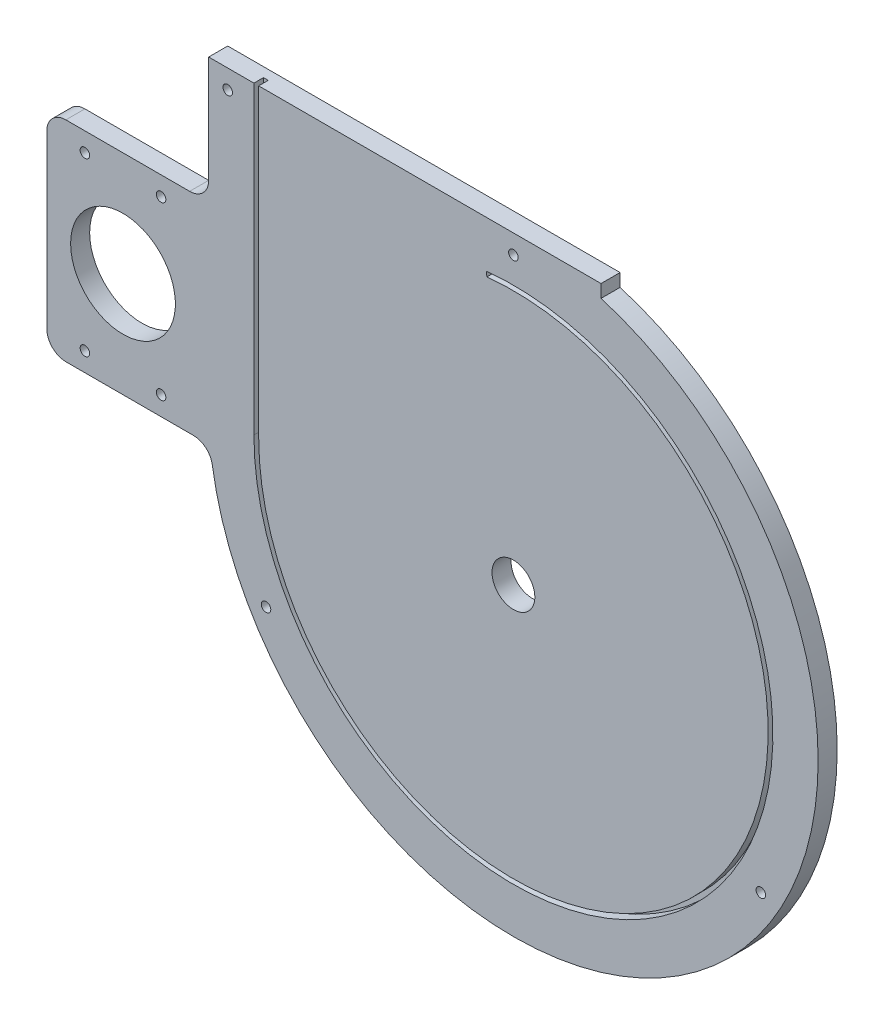
SolidWorks part; units mm, degrees
ref_plane "Front Plane" through (0, 0, 0) normal (0, 0, 1) x (1, 0, 0)
ref_plane "Top Plane" through (0, 0, 0) normal (0, 1, 0) x (1, 0, 0)
ref_plane "Right Plane" through (0, 0, 0) normal (1, 0, 0) x (0, 0, -1)
sketch "Sketch1" plane through (0, 0, 0) normal (0, 0, 1) x (1, 0, 0)
  line L1 (203.2, -203.2) -> (-203.2, -203.2)
  line L2 (203.2, -203.2) -> (203.2, 203.2)
  line L3 (203.2, 203.2) -> (-203.2, 203.2)
  line L4 (-203.2, -203.2) -> (-203.2, 203.2)
  line L5 (203.2, -203.2) -> (-203.2, 203.2) construction
  line L6 (203.2, 203.2) -> (-203.2, -203.2) construction
  circle A0 centre (0, 0) radius 14.2875
  circle A1 centre (0, 0) radius 160.3375 construction
  circle A2 centre (0, 0) radius 50.8 construction
  point P0 (0, 0)
  dimension "D3" = 28.575
  dimension "D4" = 101.6
  dimension "D1" = 406.4
  dimension "D2" = 406.4
  dimension "D5" = 203.2
  dimension "D6" = 203.2
extrude "Boss-Extrude1" add sketch "Sketch1" along normal blind 12.7
sketch "Sketch2" plane through (0, 0, 12.7) normal (0, 0, 1) x (1, 0, 0)
  line L0 (-18.0277, 172.0958) -> (-17.6969, 168.9381)
  line L1 (-173.0375, 0) -> (-173.0375, 203.2)
  line L2 (-169.8625, 0) -> (-169.8625, 203.2)
  line L3 (-169.8625, 203.2) -> (-173.0375, 203.2)
  line L4 (203.2, 203.2) -> (-203.2, 203.2) construction
  line L5 (0, 0) -> (-139.4589, -105.0957) construction
  arc A0 (-18.0277, 172.0958) -> (-173.0375, 0) centre (0, 0) cw
  arc A1 (-17.6969, 168.9381) -> (-169.8625, 0) centre (0, 0) cw
  circle A2 centre (0, 0) radius 14.2875 construction
  circle A3 centre (0, 0) radius 50.8 construction
  circle A4 centre (-90.0144, -67.8345) radius 61.9125 construction
  circle A5 centre (0, 0) radius 169.8625 construction
  point P13 (-138.1911, -104.1403)
  dimension "D2" = 101.6
  dimension "D3" = 123.825
  dimension "D4" = 1.5875
  dimension "D1" = 3.175
extrude "Cut-Extrude1" cut sketch "Sketch2" against normal blind 6.35
sketch "Sketch3" plane through (0, 0, 12.7) normal (0, 0, 1) x (1, 0, 0)
  line L0 (-203.2, 203.2) -> (-203.2, -203.2) construction
  line L1 (58.4327, 194.6172) -> (58.4327, 203.2)
  line L2 (203.2, 203.2) -> (-169.8625, 203.2) construction
  line L3 (58.4327, 203.2) -> (203.2, 203.2)
  line L4 (-203.2, -203.2) -> (203.2, -203.2) construction
  line L5 (203.2, -203.2) -> (203.2, 203.2) construction
  line L6 (-203.2, 0) -> (-203.2, -203.2)
  line L7 (-203.2, -203.2) -> (203.2, -203.2)
  line L8 (203.2, -203.2) -> (203.2, 203.2)
  arc A0 (-203.2, 0) -> (58.4327, 194.6172) centre (0, 0) ccw
  line M4 (-203.2, 203.2) -> (-203.2, -203.2)
  line M5 (-203.2, -203.2) -> (203.2, -203.2)
  line M6 (203.2, -203.2) -> (203.2, 203.2)
  line M7 (203.2, 203.2) -> (-169.8625, 203.2)
extrude "Cut-Extrude2" cut sketch "Sketch3" against normal through all contours A0 L8 L1 M7 | A0 L7 M6 | A0 M4 M5
sketch "Sketch4" plane through (0, 0, 12.7) normal (0, 0, 1) x (1, 0, 0)
  line L0 (-203.2, 203.2) -> (-203.2, 0) construction
  line L1 (-173.0375, 203.2) -> (-203.2, 203.2) construction
  line L2 (-164.9778, -95.25) -> (0, 190.5) construction
  line L3 (0, 190.5) -> (164.9778, -95.25) construction
  line L4 (164.9778, -95.25) -> (-164.9778, -95.25) construction
  circle A0 centre (-190.5, 190.5) radius 3.175
  circle A1 centre (-164.9778, -95.25) radius 3.175
  circle A2 centre (164.9778, -95.25) radius 3.175
  circle A3 centre (0, 190.5) radius 3.175
  circle A4 centre (0, 0) radius 190.5 construction
  arc A6 (-203.2, 0) -> (58.4327, 194.6172) centre (0, 0) ccw construction
  dimension "D1" = 6.35
  dimension "D4" = 12.7
  dimension "D2" = 12.7
  dimension "D3" = 12.7
extrude "Cut-Extrude3" cut sketch "Sketch4" against normal through all and the other way through all
sketch "Sketch6" plane through (0, 0, 0) normal (0, 0, -1) x (-1, 0, 0)
  line L0 (260.35, 119.2755) -> (260.35, -20.4245) construction
  line L1 (202.1709, 119.2755) -> (311.15, 119.2755)
  line L2 (202.1709, 119.2755) -> (202.1709, -20.4245)
  line L3 (202.1709, -20.4245) -> (311.15, -20.4245)
  line L4 (311.15, 119.2755) -> (311.15, -20.4245)
  line L5 (0, 0) -> (260.35, 49.4255) construction
  line L6 (203.2, 203.2) -> (203.2, 0) construction
  line L7 (203.2, 203.2) -> (203.2, 0) construction
  line L8 (285.75, 106.5755) -> (234.95, 106.5755) construction
  line L9 (285.75, 106.5755) -> (285.75, -7.7245) construction
  line L10 (285.75, -7.7245) -> (234.95, -7.7245) construction
  line L11 (234.95, 106.5755) -> (234.95, -7.7245) construction
  line L12 (285.75, 106.5755) -> (234.95, -7.7245) construction
  line L13 (285.75, -7.7245) -> (234.95, 106.5755) construction
  circle A0 centre (260.35, 49.4255) radius 34.925
  circle A1 centre (234.95, 106.5755) radius 3.175
  arc A2 (-58.4327, 194.6172) -> (203.2, 0) centre (0, 0) ccw construction
  circle A3 centre (285.75, 106.5755) radius 3.175
  circle A4 centre (285.75, -7.7245) radius 3.175
  circle A5 centre (234.95, -7.7245) radius 3.175
  point P11 (260.35, 49.4255)
  dimension "D2" = 69.85
  dimension "D6" = 6.35
  dimension "D1" = 265
  dimension "D3" = 139.7
  dimension "D4" = 107.95
  dimension "D5" = 57.15
  dimension "D7" = 50.8
  dimension "D8" = 114.3
extrude "Boss-Extrude2" add sketch "Sketch6" against normal through all
fillet "Fillet1" radius 12.7 4 edges at (-202.1709, -20.4245, 6.35) (-203.2, 119.2755, 6.35) (-311.15, -20.4245, 6.35) (-311.15, 119.2755, 6.35)
